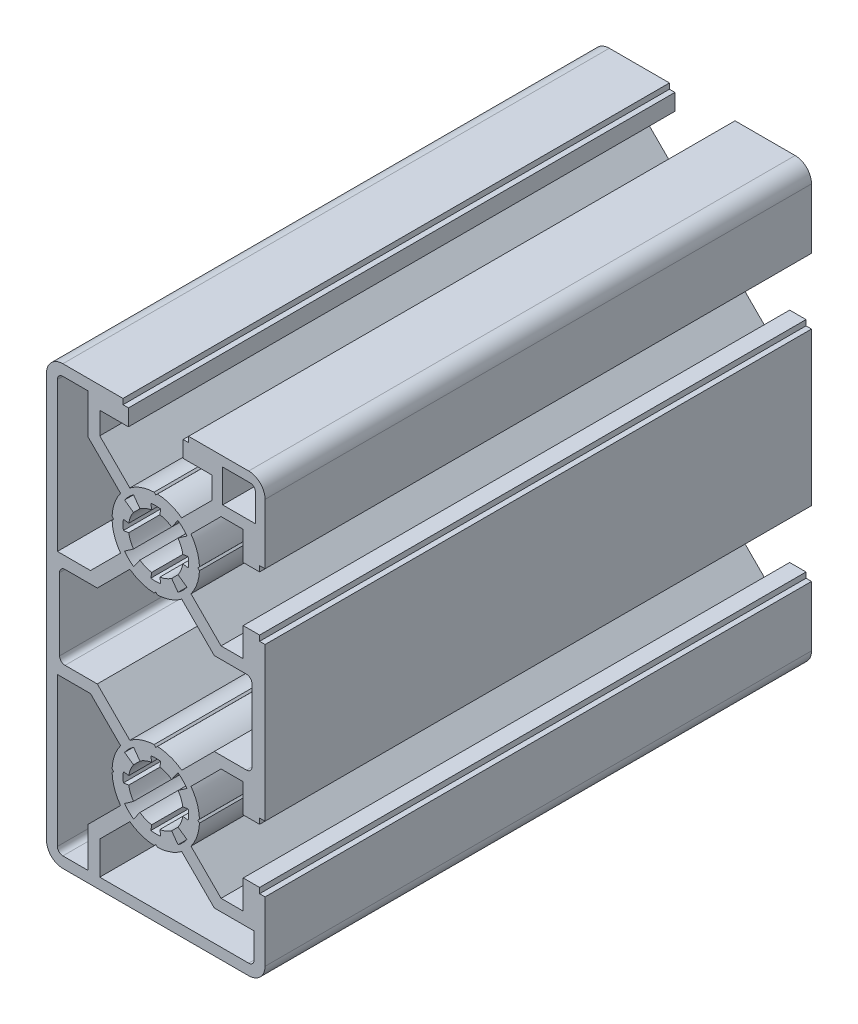
SolidWorks part; units mm, degrees
ref_plane "Ön Düzlem" through (0, 0, 0) normal (0, 0, 1) x (1, 0, 0)
ref_plane "Üst Düzlem" through (0, 0, 0) normal (0, 1, 0) x (1, 0, 0)
ref_plane "Sağ Düzlem" through (0, 0, 0) normal (1, 0, 0) x (0, 0, -1)
ref_plane "Düzlem1" through (0, 0, 100) normal (0, 0, 1) x (1, 0, 0)
sketch "Çizim1" plane through (0, 0, 100) normal (0, 0, 1) x (1, 0, 0)
  line L0 (-5.7057, 15.9448) -> (-4.0755, 17.1034)
  line L1 (-4.9435, 19.2506) -> (-5.9322, 19.1007)
  line L2 (-5.9322, 20.8993) -> (-4.9435, 20.7494)
  line L3 (-4.0755, 22.8966) -> (-5.7057, 24.0552)
  line L4 (-4.0641, 25.6994) -> (-2.903, 24.071)
  line L5 (-0.7494, 24.9435) -> (-0.8993, 25.9322)
  line L6 (0.8993, 25.9322) -> (0.7494, 24.9435)
  line L7 (2.903, 24.071) -> (4.0641, 25.6994)
  line L8 (5.7057, 24.0552) -> (4.0755, 22.8966)
  line L9 (4.9435, 20.7494) -> (5.9322, 20.8993)
  line L10 (5.9322, 19.1007) -> (4.9435, 19.2506)
  line L11 (4.0755, 17.1034) -> (5.7057, 15.9448)
  line L12 (4.0641, 14.3006) -> (2.903, 15.929)
  line L13 (0.7494, 15.0565) -> (0.8993, 14.0678)
  line L14 (-0.8993, 14.0678) -> (-0.7494, 15.0565)
  line L15 (-2.903, 15.929) -> (-4.0641, 14.3006)
  line L16 (-5.7057, -24.0552) -> (-4.0755, -22.8966)
  line L17 (-4.9435, -20.7494) -> (-5.9322, -20.8993)
  line L18 (-5.9322, -19.1007) -> (-4.9435, -19.2506)
  line L19 (-4.0755, -17.1034) -> (-5.7057, -15.9448)
  line L20 (-4.0641, -14.3006) -> (-2.903, -15.929)
  line L21 (-0.7494, -15.0565) -> (-0.8993, -14.0678)
  line L22 (0.8993, -14.0678) -> (0.7494, -15.0565)
  line L23 (2.903, -15.929) -> (4.0641, -14.3006)
  line L24 (5.7057, -15.9448) -> (4.0755, -17.1034)
  line L25 (4.9435, -19.2506) -> (5.9322, -19.1007)
  line L26 (5.9322, -20.8993) -> (4.9435, -20.7494)
  line L27 (4.0755, -22.8966) -> (5.7057, -24.0552)
  line L28 (4.0641, -25.6994) -> (2.903, -24.071)
  line L29 (0.7494, -24.9435) -> (0.8993, -25.9322)
  line L30 (-0.8993, -25.9322) -> (-0.7494, -24.9435)
  line L31 (-2.903, -24.071) -> (-4.0641, -25.6994)
  line L32 (18.25, 32.25) -> (12.25, 32.25)
  line L33 (12.25, 32.25) -> (12.25, 38.25)
  line L34 (12.25, 38.25) -> (17.25, 38.25)
  line L35 (18.25, 37.25) -> (18.25, 32.25)
  line L36 (20, 26) -> (20, 37)
  line L37 (17, 40) -> (6, 40)
  line L38 (6, 40) -> (6, 39)
  line L39 (6, 39) -> (5, 39)
  line L40 (5, 39) -> (5, 36)
  line L41 (5, 36) -> (10.25, 36)
  line L42 (10.25, 36) -> (10.25, 31.9471)
  line L43 (10.25, 31.9471) -> (4.7443, 26.4414)
  line L44 (0.3064, 27.9941) -> (0, 27.7)
  line L45 (0, 27.7) -> (-0.3064, 27.9941)
  line L46 (-4.7443, 26.4414) -> (-10.25, 31.9471)
  line L47 (-10.25, 31.9471) -> (-10.25, 36)
  line L48 (-10.25, 36) -> (-5, 36)
  line L49 (-5, 36) -> (-5, 39)
  line L50 (-5, 39) -> (-6, 39)
  line L51 (-6, 39) -> (-6, 40)
  line L52 (-6, 40) -> (-17, 40)
  line L53 (-20, 37) -> (-20, -37)
  line L54 (-17, -40) -> (17, -40)
  line L55 (20, -37) -> (20, -26)
  line L56 (20, -26) -> (19, -26)
  line L57 (19, -26) -> (19, -25)
  line L58 (19, -25) -> (16, -25)
  line L59 (16, -25) -> (16, -30.25)
  line L60 (16, -30.25) -> (11.9471, -30.25)
  line L61 (11.9471, -30.25) -> (6.4414, -24.7443)
  line L62 (7.9941, -20.3064) -> (7.7, -20)
  line L63 (7.7, -20) -> (7.9941, -19.6936)
  line L64 (6.4414, -15.2557) -> (11.9471, -9.75)
  line L65 (11.9471, -9.75) -> (16, -9.75)
  line L66 (16, -9.75) -> (16, -15)
  line L67 (16, -15) -> (19, -15)
  line L68 (19, -15) -> (19, -14)
  line L69 (19, -14) -> (20, -14)
  line L70 (20, -14) -> (20, 14)
  line L71 (20, 14) -> (19, 14)
  line L72 (19, 14) -> (19, 15)
  line L73 (19, 15) -> (16, 15)
  line L74 (16, 15) -> (16, 9.75)
  line L75 (16, 9.75) -> (11.9471, 9.75)
  line L76 (11.9471, 9.75) -> (6.4414, 15.2557)
  line L77 (7.9941, 19.6936) -> (7.7, 20)
  line L78 (7.7, 20) -> (7.9941, 20.3064)
  line L79 (6.4414, 24.7443) -> (11.9471, 30.25)
  line L80 (11.9471, 30.25) -> (16, 30.25)
  line L81 (16, 30.25) -> (16, 25)
  line L82 (16, 25) -> (19, 25)
  line L83 (19, 25) -> (19, 26)
  line L84 (19, 26) -> (20, 26)
  line L85 (-11.9471, 9.75) -> (-18, 9.75)
  line L86 (-18, 9.75) -> (-18, 37)
  line L87 (-17, 38) -> (-12.4, 38)
  line L88 (-12.4, 38) -> (-12.4, 30.7029)
  line L89 (-12.4, 30.7029) -> (-6.4414, 24.7443)
  line L90 (-7.9941, 20.3064) -> (-7.7, 20)
  line L91 (-7.7, 20) -> (-7.9941, 19.6936)
  line L92 (-6.4414, 15.2557) -> (-11.9471, 9.75)
  line L93 (-18, -9.75) -> (-11.9471, -9.75)
  line L94 (-11.9471, -9.75) -> (-6.4414, -15.2557)
  line L95 (-7.9941, -19.6936) -> (-7.7, -20)
  line L96 (-7.7, -20) -> (-7.9941, -20.3064)
  line L97 (-6.4414, -24.7443) -> (-12.4, -30.7029)
  line L98 (-12.4, -30.7029) -> (-12.4, -38)
  line L99 (-12.4, -38) -> (-17, -38)
  line L100 (-18, -37) -> (-18, -9.75)
  line L101 (-10.25, -38) -> (-10.25, -31.9471)
  line L102 (-10.25, -31.9471) -> (-4.7443, -26.4414)
  line L103 (-0.3064, -27.9941) -> (0, -27.7)
  line L104 (0, -27.7) -> (0.3064, -27.9941)
  line L105 (4.7443, -26.4414) -> (10.7029, -32.4)
  line L106 (10.7029, -32.4) -> (18, -32.4)
  line L107 (18, -32.4) -> (18, -37)
  line L108 (17, -38) -> (-10.25, -38)
  line L109 (-16.6, 7.6) -> (-10.7029, 7.6)
  line L110 (-10.7029, 7.6) -> (-4.7443, 13.5586)
  line L111 (-0.3064, 12.0059) -> (0, 12.3)
  line L112 (0, 12.3) -> (0.3064, 12.0059)
  line L113 (4.7443, 13.5586) -> (10.7029, 7.6)
  line L114 (10.7029, 7.6) -> (16.6, 7.6)
  line L115 (17.6, 6.6) -> (17.6, -6.6)
  line L116 (16.6, -7.6) -> (10.7029, -7.6)
  line L117 (10.7029, -7.6) -> (4.7443, -13.5586)
  line L118 (0.3064, -12.0059) -> (0, -12.3)
  line L119 (0, -12.3) -> (-0.3064, -12.0059)
  line L120 (-4.7443, -13.5586) -> (-10.7029, -7.6)
  line L121 (-10.7029, -7.6) -> (-16.6, -7.6)
  line L122 (-17.6, -6.6) -> (-17.6, 6.6)
  arc A0 (-4.0755, 17.1034) -> (-4.9435, 19.2506) centre (0, 20) cw
  arc A1 (-5.9322, 19.1007) -> (-5.9322, 20.8993) centre (0, 20) cw
  arc A2 (-4.9435, 20.7494) -> (-4.0755, 22.8966) centre (0, 20) cw
  arc A3 (-5.7057, 24.0552) -> (-4.0641, 25.6994) centre (0, 20) cw
  arc A4 (-2.903, 24.071) -> (-0.7494, 24.9435) centre (0, 20) cw
  arc A5 (-0.8993, 25.9322) -> (0.8993, 25.9322) centre (0, 20) cw
  arc A6 (0.7494, 24.9435) -> (2.903, 24.071) centre (0, 20) cw
  arc A7 (4.0641, 25.6994) -> (5.7057, 24.0552) centre (0, 20) cw
  arc A8 (4.0755, 22.8966) -> (4.9435, 20.7494) centre (0, 20) cw
  arc A9 (5.9322, 20.8993) -> (5.9322, 19.1007) centre (0, 20) cw
  arc A10 (4.9435, 19.2506) -> (4.0755, 17.1034) centre (0, 20) cw
  arc A11 (5.7057, 15.9448) -> (4.0641, 14.3006) centre (0, 20) cw
  arc A12 (2.903, 15.929) -> (0.7494, 15.0565) centre (0, 20) cw
  arc A13 (0.8993, 14.0678) -> (-0.8993, 14.0678) centre (0, 20) cw
  arc A14 (-0.7494, 15.0565) -> (-2.903, 15.929) centre (0, 20) cw
  arc A15 (-4.0641, 14.3006) -> (-5.7057, 15.9448) centre (0, 20) cw
  arc A16 (-4.0755, -22.8966) -> (-4.9435, -20.7494) centre (0, -20) cw
  arc A17 (-5.9322, -20.8993) -> (-5.9322, -19.1007) centre (0, -20) cw
  arc A18 (-4.9435, -19.2506) -> (-4.0755, -17.1034) centre (0, -20) cw
  arc A19 (-5.7057, -15.9448) -> (-4.0641, -14.3006) centre (0, -20) cw
  arc A20 (-2.903, -15.929) -> (-0.7494, -15.0565) centre (0, -20) cw
  arc A21 (-0.8993, -14.0678) -> (0.8993, -14.0678) centre (0, -20) cw
  arc A22 (0.7494, -15.0565) -> (2.903, -15.929) centre (0, -20) cw
  arc A23 (4.0641, -14.3006) -> (5.7057, -15.9448) centre (0, -20) cw
  arc A24 (4.0755, -17.1034) -> (4.9435, -19.2506) centre (0, -20) cw
  arc A25 (5.9322, -19.1007) -> (5.9322, -20.8993) centre (0, -20) cw
  arc A26 (4.9435, -20.7494) -> (4.0755, -22.8966) centre (0, -20) cw
  arc A27 (5.7057, -24.0552) -> (4.0641, -25.6994) centre (0, -20) cw
  arc A28 (2.903, -24.071) -> (0.7494, -24.9435) centre (0, -20) cw
  arc A29 (0.8993, -25.9322) -> (-0.8993, -25.9322) centre (0, -20) cw
  arc A30 (-0.7494, -24.9435) -> (-2.903, -24.071) centre (0, -20) cw
  arc A31 (-4.0641, -25.6994) -> (-5.7057, -24.0552) centre (0, -20) cw
  arc A32 (17.25, 38.25) -> (18.25, 37.25) centre (17.25, 37.25) cw
  arc A33 (20, 37) -> (17, 40) centre (17, 37) ccw
  arc A34 (4.7443, 26.4414) -> (0.3064, 27.9941) centre (0, 20) ccw
  arc A35 (-0.3064, 27.9941) -> (-4.7443, 26.4414) centre (0, 20) ccw
  arc A36 (-17, 40) -> (-20, 37) centre (-17, 37) ccw
  arc A37 (-20, -37) -> (-17, -40) centre (-17, -37) ccw
  arc A38 (17, -40) -> (20, -37) centre (17, -37) ccw
  arc A39 (6.4414, -24.7443) -> (7.9941, -20.3064) centre (0, -20) ccw
  arc A40 (7.9941, -19.6936) -> (6.4414, -15.2557) centre (0, -20) ccw
  arc A41 (6.4414, 15.2557) -> (7.9941, 19.6936) centre (0, 20) ccw
  arc A42 (7.9941, 20.3064) -> (6.4414, 24.7443) centre (0, 20) ccw
  arc A43 (-18, 37) -> (-17, 38) centre (-17, 37) cw
  arc A44 (-6.4414, 24.7443) -> (-7.9941, 20.3064) centre (0, 20) ccw
  arc A45 (-7.9941, 19.6936) -> (-6.4414, 15.2557) centre (0, 20) ccw
  arc A46 (-6.4414, -15.2557) -> (-7.9941, -19.6936) centre (0, -20) ccw
  arc A47 (-7.9941, -20.3064) -> (-6.4414, -24.7443) centre (0, -20) ccw
  arc A48 (-17, -38) -> (-18, -37) centre (-17, -37) cw
  arc A49 (-4.7443, -26.4414) -> (-0.3064, -27.9941) centre (0, -20) ccw
  arc A50 (0.3064, -27.9941) -> (4.7443, -26.4414) centre (0, -20) ccw
  arc A51 (18, -37) -> (17, -38) centre (17, -37) cw
  arc A52 (-17.6, 6.6) -> (-16.6, 7.6) centre (-16.6, 6.6) cw
  arc A53 (-4.7443, 13.5586) -> (-0.3064, 12.0059) centre (0, 20) ccw
  arc A54 (0.3064, 12.0059) -> (4.7443, 13.5586) centre (0, 20) ccw
  arc A55 (16.6, 7.6) -> (17.6, 6.6) centre (16.6, 6.6) cw
  arc A56 (17.6, -6.6) -> (16.6, -7.6) centre (16.6, -6.6) cw
  arc A57 (4.7443, -13.5586) -> (0.3064, -12.0059) centre (0, -20) ccw
  arc A58 (-0.3064, -12.0059) -> (-4.7443, -13.5586) centre (0, -20) ccw
  arc A59 (-16.6, -7.6) -> (-17.6, -6.6) centre (-16.6, -6.6) cw
extrude "Yükseklik-Ekstrüzyon1" add sketch "Çizim1" against normal blind 100
